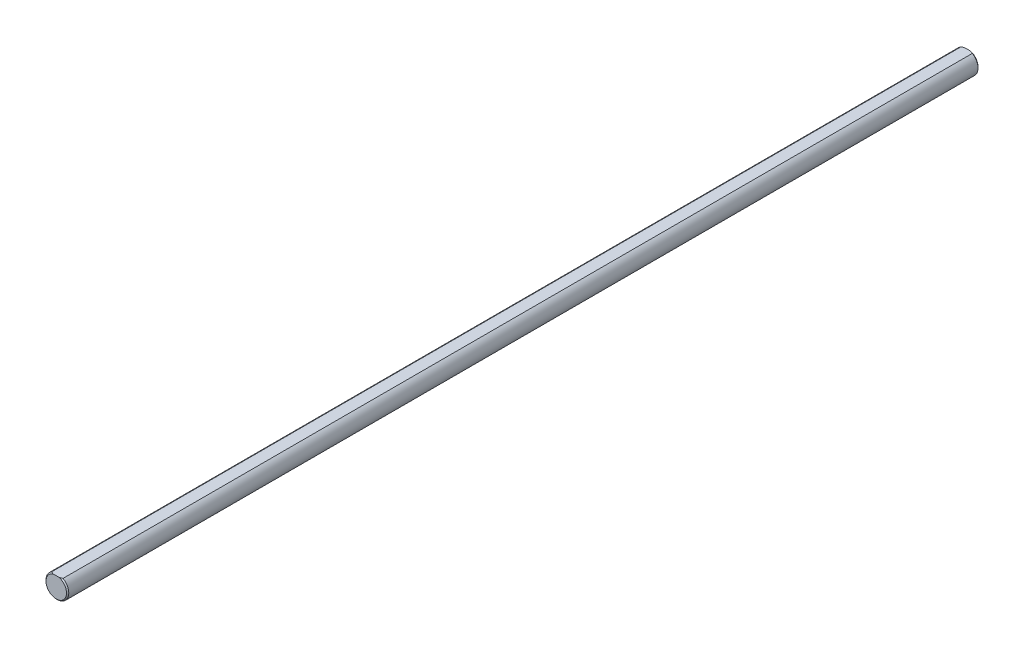
SolidWorks part; units mm, degrees
material "Plain Carbon Steel"
ref_plane "Front Plane" through (0, 0, 0) normal (0, 0, 1) x (1, 0, 0)
ref_plane "Top Plane" through (0, 0, 0) normal (0, 1, 0) x (1, 0, 0)
ref_plane "Right Plane" through (0, 0, 0) normal (1, 0, 0) x (0, 0, -1)
sketch "Sketch1" plane through (0, 0, 0) normal (0, 0, 1) x (1, 0, 0)
  line L0 (2.5, 4.3301) -> (-2.5, 4.3301) construction
  line L1 (0, 4.3301) -> (0, 0) construction
  line L2 (0, 0) -> (0, -5) construction
  circle A1 centre (0, 0) radius 5 construction
  dimension "Diameter" = 10
  dimension "Flat Width" = 5
  dimension "D1" = 9.3301
sketch "Sketch2" plane through (0, 0, 0) normal (1, 0, 0) x (0, 0, -1)
  line L0 (-200, 5) -> (200, 5) construction
  line L1 (0, 5) -> (0, -5) construction
  line L2 (0, 5) -> (0, -5) construction
  line L3 (-200, 5) -> (-200, 0) construction
  line L4 (-200, 0) -> (0, 0) construction
  line L6 (-200, 4.5) -> (-199.5, 5) construction
  point P2 (0, 5)
  point P3 (180, 5)
  point P4 (-180, 5)
  dimension "Length/ D-Profile Length" = 400
  dimension "D2" = 20
  dimension "D1" = 20
  dimension "Chamfer Typ." = 45
  dimension "D4" = 0.5
sketch "Sketch3" plane through (0, 0, 0) normal (0, 0, 1) x (1, 0, 0)
  circle A1 centre (0, 0) radius 5 construction
  circle A3 centre (0, 0) radius 5
extrude "Boss-Extrude2" add sketch "Sketch3" along normal up to vertex (200 mm away) and the other way up to vertex (200 mm away) up to point (0, 5, 200) other way up to point (0, 5, -200)
sketch "Sketch10" plane through (0, 0, 0) normal (0, 0, 1) x (1, 0, 0)
  line L0 (-2.5, 4.3301) -> (2.5, 4.3301)
  line L1 (0, 0) -> (0, 5) construction
  circle A0 centre (0, 0) radius 5 construction
  circle A1 centre (0, 0) radius 5 construction
  arc A2 (-2.5, 4.3301) -> (2.5, 4.3301) centre (0, 0) cw
extrude "Cut-Extrude5" cut sketch "Sketch10" against normal through all both and the other way through all
chamfer "Chamfer1" distance 0.5 angle 45 4 edges at (0, -5, 200) (0, -5, -200) (0, 4.3301, -200) (0, 4.3301, 200)
equation "\"D1@Chamfer1\"= \"Diameter@Sketch1\" / 20"
equation "\"D1@Sketch2\"=\"Diameter@Sketch1\"*2"
equation "\"D2@Sketch2\"=\"D1@Sketch2\""
equation "\"D4@Sketch2\"=\"Diameter@Sketch1\" / 20"
